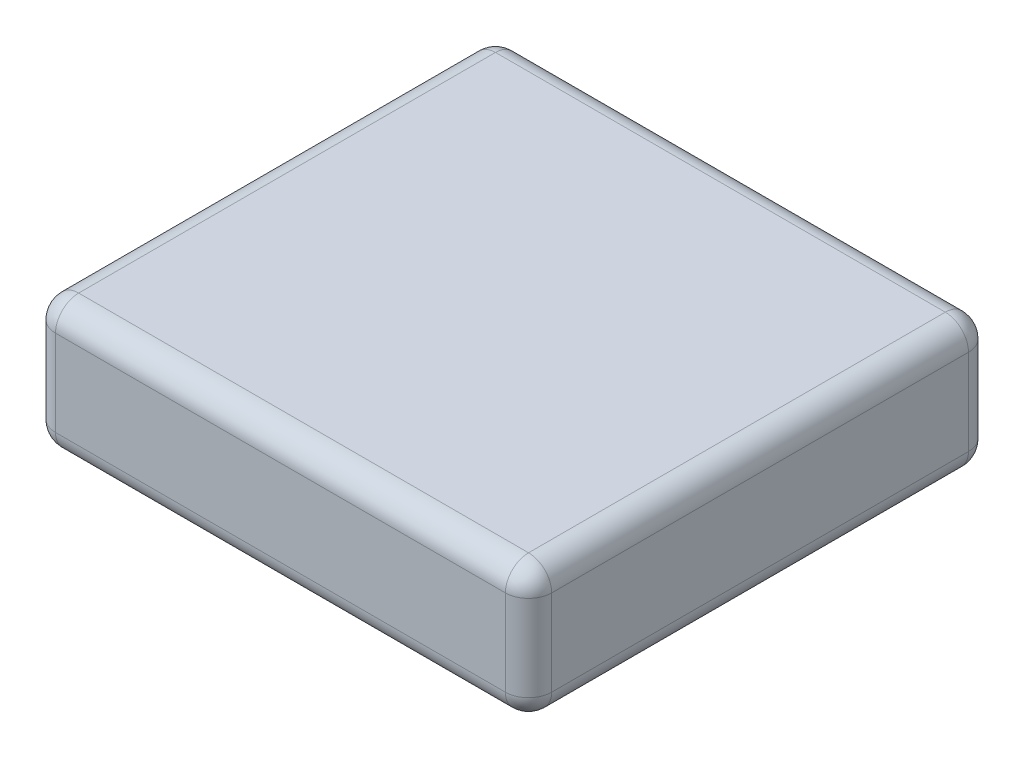
SolidWorks part; units mm, degrees
ref_plane "Front Plane" through (0, 0, 0) normal (0, 0, 1) x (1, 0, 0)
ref_plane "Top Plane" through (0, 0, 0) normal (0, 1, 0) x (1, 0, 0)
ref_plane "Right Plane" through (0, 0, 0) normal (1, 0, 0) x (0, 0, -1)
sketch "Sketch1" plane through (0, 0, 0) normal (0, 1, 0) x (1, 0, 0)
  line L1 (-243.4473, 350) -> (506.5527, 350)
  line L2 (-243.4473, 350) -> (-243.4473, -350)
  line L3 (-243.4473, -350) -> (506.5527, -350)
  line L4 (506.5527, 350) -> (506.5527, -350)
  line L5 (-243.4473, 350) -> (506.5527, -350) construction
  line L6 (-243.4473, -350) -> (506.5527, 350) construction
  point P0 (0, 0)
  point P5 (-243.4473, -350)
  dimension "D1" = 700
  dimension "D2" = 750
extrude "Boss-Extrude1" add sketch "Sketch1" along normal blind 200
fillet "Fillet1" radius 35 12 edges at (506.5527, 100, -350) (-243.4473, 100, -350) (-243.4473, 100, 350) (506.5527, 100, 350) (131.5527, 200, 350) (-243.4473, 200, 0) (131.5527, 200, -350) (506.5527, 200, 0) (131.5527, 0, -350) (-243.4473, 0, 0) (131.5527, 0, 350) (506.5527, 0, 0)
